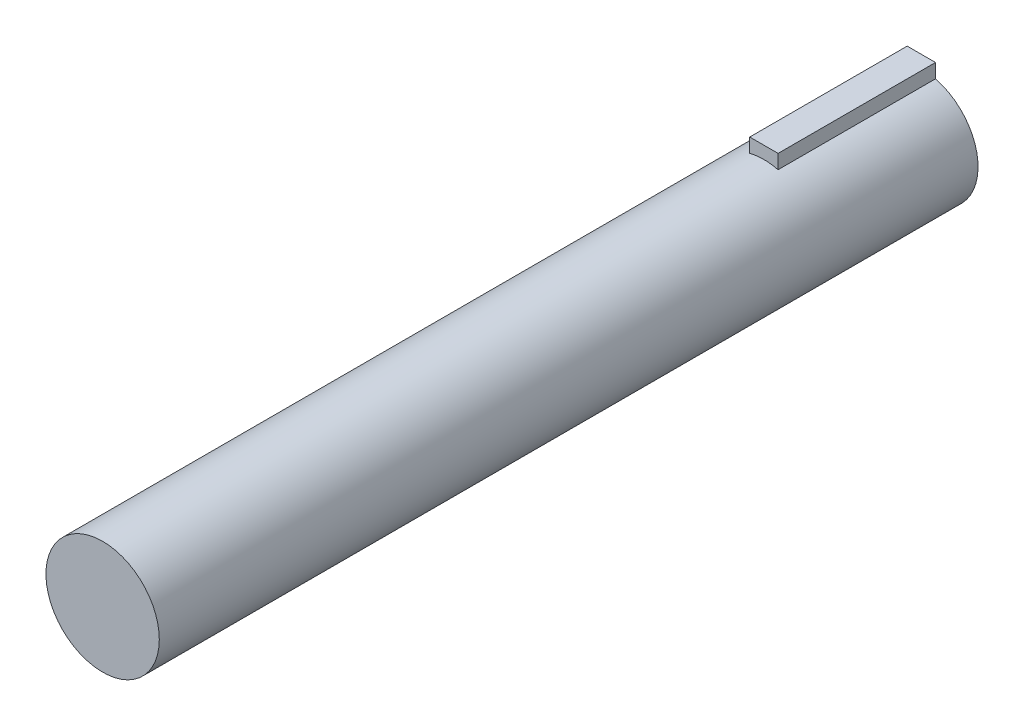
SolidWorks part; units mm, degrees
material "AISI 1020"
ref_plane "Front Plane" through (0, 0, 0) normal (0, 0, 1) x (1, 0, 0)
ref_plane "Top Plane" through (0, 0, 0) normal (0, 1, 0) x (1, 0, 0)
ref_plane "Right Plane" through (0, 0, 0) normal (1, 0, 0) x (0, 0, -1)
sketch "Sketch1" plane through (0, 0, 0) normal (0, 0, 1) x (1, 0, 0)
  circle A0 centre (0, 0) radius 4.572
  dimension "D1" = 9.144
extrude "Boss-Extrude1" add sketch "Sketch1" along normal blind 66.04
sketch "Sketch3" plane through (0, 0, 0) normal (0, 0, -1) x (-1, 0, 0)
  line L1 (-1.143, 5.5698) -> (1.143, 5.5698)
  line L2 (-1.143, 5.5698) -> (-1.143, 3.2838)
  line L3 (-1.143, 3.2838) -> (1.143, 3.2838)
  line L4 (1.143, 5.5698) -> (1.143, 3.2838)
  circle A0 centre (0, 0) radius 4.572 construction
  point P4 (0, 3.2838)
  point P6 (-1.143, 4.4268)
  dimension "D1" = 2.286
  dimension "D2" = 2.286
extrude "Boss-Extrude3" add sketch "Sketch3" against normal blind 12.7
